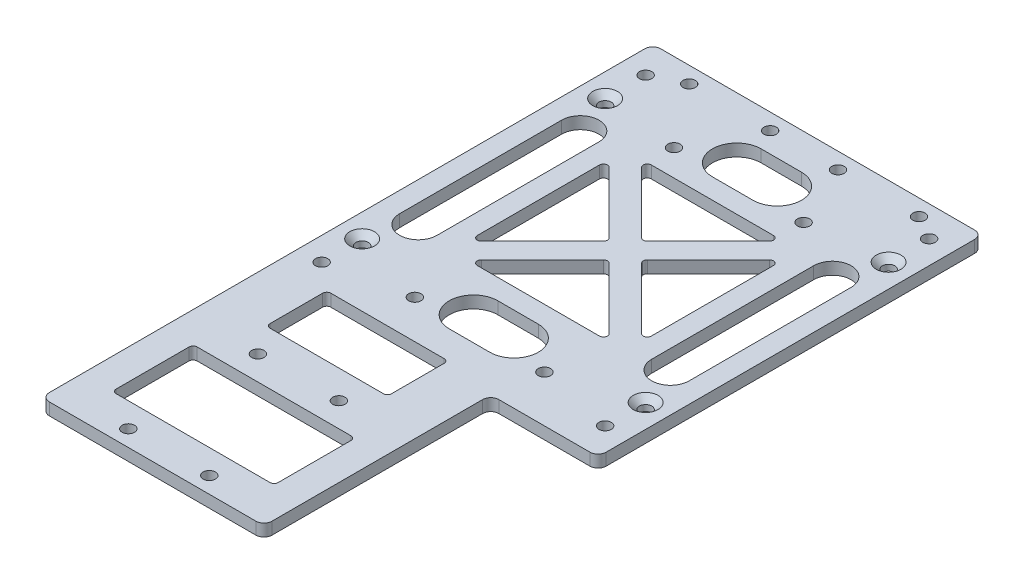
SolidWorks part; units mm, degrees
material "Thornel Mat VMA"
ref_plane "前视基准面" through (0, 0, 0) normal (0, 0, 1) x (1, 0, 0)
ref_plane "上视基准面" through (0, 0, 0) normal (0, 1, 0) x (1, 0, 0)
ref_plane "右视基准面" through (0, 0, 0) normal (1, 0, 0) x (0, 0, -1)
other "Configuration Table"
sketch "草图1" plane through (0, 0, 0) normal (0, 1, 0) x (1, 0, 0)
  line L0 (0, 0) -> (33, 0) construction
  line L1 (33, 0) -> (33, 40)
  line L2 (33, 40) -> (-55, 40)
  line L3 (-55, 40) -> (-55, -111)
  line L4 (-55, -111) -> (0, -111)
  line L5 (0, -111) -> (0, 0)
  line L6 (0, -55) -> (33, -55)
  line L7 (33, -55) -> (33, 0)
  dimension "D1" = 55
  dimension "D2" = 40
  dimension "D3" = 151
  dimension "D4" = 88
  dimension "D5" = 55
extrude "凸台-拉伸1" add sketch "草图1" along normal blind 3 contours L5 L0 L1 L2 L3 L4 | L0 L5 L6 L7
sketch "草图2" plane through (0, 3, 0) normal (0, 1, 0) x (1, 0, 0)
  line L0 (33, 40) -> (-55, 40) construction
  line L1 (-55, -111) -> (0, -111) construction
  line L2 (0, -55) -> (33, -55) construction
  line L3 (-11, 40) -> (-11, 35) construction
  line L4 (-27.5, -111) -> (-27.5, -101) construction
  line L5 (-55, 40) -> (-55, -111) construction
  circle A0 centre (-37.5, -107) radius 1.525
  circle A1 centre (-17.5, -107) radius 1.525
  circle A2 centre (-37.5, -75) radius 1.525
  circle A3 centre (-17.5, -75) radius 1.525
  circle A4 centre (-42, 36) radius 1.525
  circle A5 centre (-22, 36) radius 1.525
  circle A6 centre (-5.25, 36) radius 1.525
  circle A7 centre (14.75, 36) radius 1.525
  dimension "D1" = 3.05
  dimension "D3" = 20
  dimension "D5" = 20
  dimension "D6" = 4
  dimension "D7" = 4
  dimension "D8" = 20
  dimension "D10" = 49.75
  dimension "D12" = 13
  dimension "D2" = 20
  dimension "D4" = 20
  dimension "D9" = 5
  dimension "D11" = 10
extrude "切除-拉伸1" cut sketch "草图2" against normal through all
sketch "草图5" plane through (0, 3, 0) normal (0, 1, 0) x (1, 0, 0)
  line L0 (0, -55) -> (33, -55) construction
  line L1 (33, 40) -> (26.5, 40)
  line L2 (33, 40) -> (33, -55)
  line L3 (33, -55) -> (26.5, -55)
  line L4 (26.5, 40) -> (26.5, -55)
  dimension "D1" = 6.5
extrude "切除-拉伸4" cut sketch "草图5" against normal through all
fillet "圆角3" radius 2 6 edges at (26.5, 1.5, 55) (0, 1.5, 55) (-55, 1.5, 111) (-55, 1.5, -40) (26.5, 1.5, -40) (0, 1.5, 111)
sketch "草图7" plane through (0, 0, 0) normal (0, -1, 0) x (1, 0, 0)
  line L0 (26.5, -38) -> (26.5, 53) construction
  line L1 (-49.25, 47.5) -> (20.75, 47.5) construction
  line L2 (-49.25, 47.5) -> (-49.25, -32.5) construction
  line L3 (-49.25, -32.5) -> (20.75, -32.5) construction
  line L4 (20.75, 47.5) -> (20.75, -32.5) construction
  line L5 (24.5, -40) -> (-53, -40) construction
  circle A0 centre (-49.25, 47.5) radius 1.525
  circle A1 centre (-49.25, -32.5) radius 1.525
  circle A2 centre (20.75, -32.5) radius 1.525
  circle A3 centre (20.75, 47.5) radius 1.525
  point P6 (26.5, 7.5)
  point P7 (20.75, 7.5)
  point P10 (-14.25, -40)
  point P11 (-14.25, -32.5)
  dimension "D3" = 3.05
  dimension "D1" = 70
  dimension "D2" = 80
extrude "切除-拉伸6" cut sketch "草图7" against normal blind 10
sketch "草图10" plane through (0, 0, 0) normal (0, -1, 0) x (1, 0, 0)
  circle A0 centre (-30.25, 43.5) radius 1.525
  circle A1 centre (1.75, 43.5) radius 1.525
  circle A2 centre (-30.2503, -20.4998) radius 1.525
  circle A3 centre (1.75, -20.5) radius 1.525
  dimension "D1" = 3.05
extrude "切除-拉伸8" cut sketch "草图10" against normal blind 10
sketch "草图14" plane through (0, 3, 0) normal (0, 1, 0) x (1, 0, 0)
  line L0 (-10.25, -7.5) -> (7.25, 10)
  line L1 (-36.75, -30) -> (8.25, -30) construction
  line L2 (-36.75, -30) -> (-36.75, 15) construction
  line L3 (-36.75, 15) -> (8.25, 15) construction
  line L4 (8.25, -30) -> (8.25, 15) construction
  line L5 (-36.75, -30) -> (8.25, 15) construction
  line L6 (-36.75, 15) -> (8.25, -30) construction
  line L7 (24.5, 40) -> (-53, 40) construction
  line L8 (26.5, 38) -> (26.5, -53) construction
  line L9 (-31.75, 14) -> (3.25, 14)
  line L10 (3.25, 14) -> (-14.25, -3.5)
  line L11 (-14.25, -3.5) -> (-31.75, 14)
  line L12 (7.25, -25) -> (-10.25, -7.5)
  line L13 (7.25, 10) -> (7.25, -25)
  line L14 (-14.25, -11.5) -> (3.25, -29)
  line L15 (-31.75, -29) -> (-14.25, -11.5)
  line L16 (3.25, -29) -> (-31.75, -29)
  line L17 (-18.25, -7.5) -> (-35.75, -25)
  line L18 (-35.75, 10) -> (-18.25, -7.5)
  line L19 (-35.75, -25) -> (-35.75, 10)
  point P0 (-14.25, -7.5)
  point P9 (-14.25, 40)
  point P10 (-14.25, 15)
  point P11 (26.5, -7.5)
  point P12 (8.25, -7.5)
  point P28 (-14.25, -7.5)
  dimension "D1" = 45
  dimension "D2" = 45
  dimension "D3" = 1
  dimension "D4" = 45
  dimension "D5" = 35
  dimension "D6" = 4
extrude "切除-拉伸9" cut sketch "草图14" against normal through all both
fillet "圆角4" radius 1 12 edges at (3.25, 1.5, -14) (-14.25, 1.5, 3.5) (-31.75, 1.5, -14) (-18.25, 1.5, 7.5) (-35.75, 1.5, -10) (-10.25, 1.5, 7.5) (7.25, 1.5, -10) (7.25, 1.5, 25) (-14.25, 1.5, 11.5) (3.25, 1.5, 29) (-31.75, 1.5, 29) (-35.75, 1.5, 25)
sketch "草图15" plane through (0, 3, 0) normal (0, 1, 0) x (1, 0, 0)
  line L0 (-17.5, -75) -> (-17.5, -107) construction
  line L1 (-47.5, -101) -> (-7.5, -101)
  line L2 (-47.5, -101) -> (-47.5, -81)
  line L3 (-47.5, -81) -> (-7.5, -81)
  line L4 (-7.5, -101) -> (-7.5, -81)
  line L5 (-47.5, -101) -> (-7.5, -81) construction
  line L6 (-47.5, -81) -> (-7.5, -101) construction
  line L7 (-42.5, -68) -> (-12.5, -68)
  line L8 (-42.5, -68) -> (-42.5, -53)
  line L9 (-42.5, -53) -> (-12.5, -53)
  line L10 (-12.5, -68) -> (-12.5, -53)
  line L11 (-42.5, -68) -> (-12.5, -53) construction
  line L12 (-42.5, -53) -> (-12.5, -68) construction
  line L13 (-53, -111) -> (-2, -111) construction
  point P0 (-27.5, -91)
  point P5 (-27.5, -60.5)
  point P14 (-17.5, -91)
  point P18 (-27.5, -111)
  dimension "D1" = 20
  dimension "D2" = 40
  dimension "D3" = 13
  dimension "D4" = 15
  dimension "D5" = 30
extrude "切除-拉伸10" cut sketch "草图15" against normal through all both
fillet "圆角5" radius 1 8 edges at (-42.5, 1.5, 53) (-12.5, 1.5, 53) (-12.5, 1.5, 68) (-47.5, 1.5, 101) (-47.5, 1.5, 81) (-7.5, 1.5, 81) (-7.5, 1.5, 101) (-42.5, 1.5, 68)
sketch "草图16" plane through (0, 3, 0) normal (0, 1, 0) x (1, 0, 0)
  line L0 (-45.375, -27.5) -> (-45.375, 12.5) construction
  line L1 (-50, -27.5) -> (-50, 12.5)
  line L2 (-40.75, -27.5) -> (-40.75, 12.5)
  line L3 (16.875, -27.5) -> (16.875, 12.5) construction
  line L4 (12.25, -27.5) -> (12.25, 12.5)
  line L5 (21.5, -27.5) -> (21.5, 12.5)
  line L6 (26.5, 38) -> (26.5, -53) construction
  line L7 (7.25, -7.5) -> (26.5, -7.5) construction
  line L8 (7.25, -22.5858) -> (7.25, 7.5858) construction
  line L9 (-55, 38) -> (-55, -109) construction
  arc A0 (-50, -27.5) -> (-40.75, -27.5) centre (-45.375, -27.5) ccw
  arc A1 (-40.75, 12.5) -> (-50, 12.5) centre (-45.375, 12.5) ccw
  arc A2 (12.25, -27.5) -> (21.5, -27.5) centre (16.875, -27.5) ccw
  arc A3 (21.5, 12.5) -> (12.25, 12.5) centre (16.875, 12.5) ccw
  point P2 (-45.375, -7.5)
  point P7 (16.875, -7.5)
  point P21 (16.875, -7.5)
  dimension "D1" = 5
  dimension "D2" = 40
  dimension "D3" = 5
sketch "草图17" plane through (0, 3, 0) normal (0, 1, 0) x (1, 0, 0)
  line L0 (-19.25, 25) -> (-9.25, 25) construction
  line L1 (-19.25, 31) -> (-9.25, 31)
  line L2 (-19.25, 19) -> (-9.25, 19)
  line L3 (0.8358, 14) -> (-29.3358, 14) construction
  line L4 (-9.8358, -7.5) -> (-18.6642, -7.5) construction
  line L5 (-19.25, -40) -> (-9.25, -40) construction
  line L6 (-19.25, -46) -> (-9.25, -46)
  line L7 (-19.25, -34) -> (-9.25, -34)
  arc A0 (-19.25, 31) -> (-19.25, 19) centre (-19.25, 25) ccw
  arc A1 (-9.25, 19) -> (-9.25, 31) centre (-9.25, 25) ccw
  arc A2 (-9.5429, -6.7929) -> (-9.5429, -8.2071) centre (-8.8358, -7.5) ccw construction
  arc A3 (-18.9571, -8.2071) -> (-18.9571, -6.7929) centre (-19.6642, -7.5) ccw construction
  arc A4 (-19.25, -46) -> (-19.25, -34) centre (-19.25, -40) cw
  arc A5 (-9.25, -34) -> (-9.25, -46) centre (-9.25, -40) cw
  point P2 (-14.25, 25)
  point P10 (-14.25, 14)
  point P20 (-14.25, -40)
  dimension "D1" = 6
  dimension "D2" = 10
  dimension "D3" = 5
extrude "切除-拉伸12" cut sketch "草图17" against normal through all both
sketch "草图19" plane through (0, 3, 0) normal (0, 1, 0) x (1, 0, 0)
  circle A0 centre (-49.25, -37.5) radius 1.525
  circle A1 centre (20.75, 22.5) radius 1.525
  circle A2 centre (-49.25, 22.5) radius 1.525
  circle A3 centre (20.75, -37.5) radius 1.525
  dimension "D1" = 3.05
extrude "切除-拉伸13" cut sketch "草图19" against normal blind 10
extrude "切除-拉伸14" cut sketch "草图16" against normal blind 10
hole_wizard "孔1" positions "3D草图1" profile "草图20" legacy
sketch3d "3D草图1"
  line L0 (20.75, 0, 37.5) -> (20.75, 3, 37.5) construction
  line L1 (-49.25, 0, -22.5) -> (-49.25, 3, -22.5) construction
  line L2 (-49.25, 0, 37.5) -> (-49.25, 3, 37.5) construction
  line L3 (20.75, 0, -22.5) -> (20.75, 3, -22.5) construction
  point P0 (20.75, 3, 37.5)
  point P4 (10.9534, -48.3, -26.7483)
  point P7 (-49.25, 3, -22.5)
  point P11 (-49.25, 3, 37.5)
  point P15 (20.75, 3, -22.5)
sketch "草图20" plane through (20.75, 3, 37.5) normal (1, 0, 0) x (0, 0, 1)
  line L0 (0, 0) -> (0, 100)
  line L1 (0, 100) -> (1.525, 100)
  line L2 (1.525, 100) -> (1.525, 1.525)
  line L3 (1.525, 1.525) -> (3.05, 0)
  line L4 (3.05, 0) -> (0, 0)
  line L5 (0, -6.4453) -> (0, 115.525) construction
  line L6 (-1.525, 1.525) -> (-3.05, 0) construction
  dimension "直径" = 3.05
  dimension "深度" = 100
  dimension "锥坑角度" = 90
  dimension "锥坑直径" = 6.1
